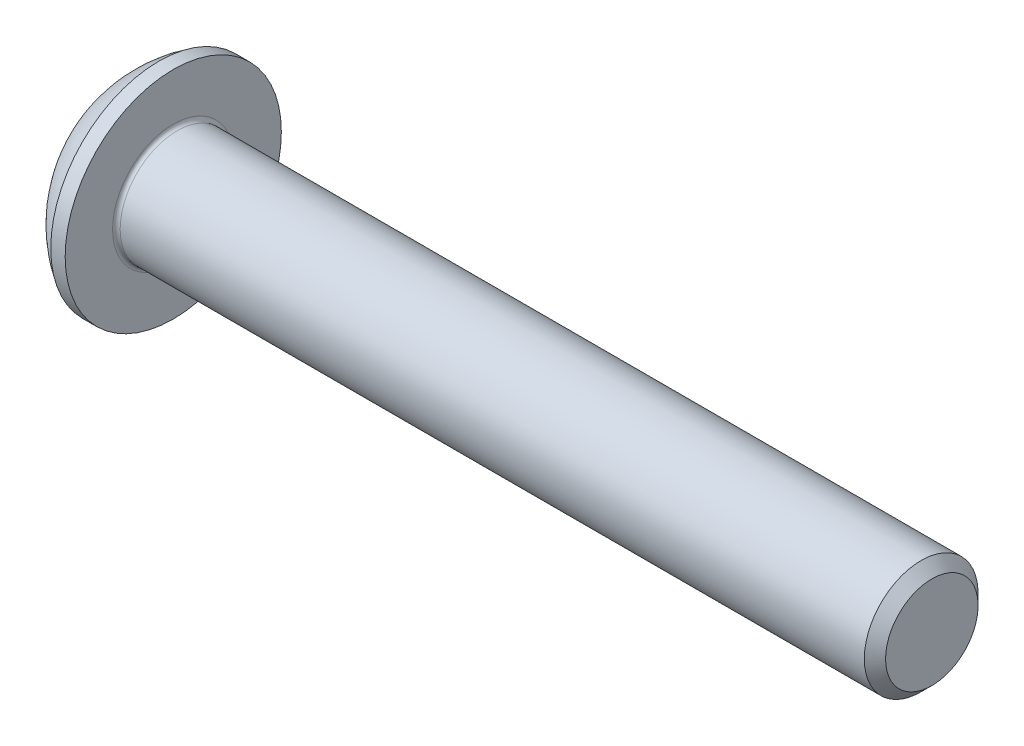
SolidWorks part; units mm, degrees
material "AISI 1035 鋼 (SS)"
ref_plane "Plane1" through (0, 0, 0) normal (0, 0, 1) x (1, 0, 0)
ref_plane "Plane2" through (0, 0, 0) normal (0, 1, 0) x (1, 0, 0)
ref_plane "Plane3" through (0, 0, 0) normal (1, 0, 0) x (0, 0, -1)
sketch "BodySke" plane through (0, 0, 0) normal (0, 0, 1) x (1, 0, 0)
  line L0 (21.65, 0) -> (21.65, 1.2195)
  line L1 (21.3695, 1.5) -> (1.65, 1.5)
  line L2 (1.65, 1.5) -> (1.65, 2.85)
  line L3 (1.65, 2.85) -> (1.27, 2.85)
  line L4 (0, 0) -> (101.6, 0) construction
  line L5 (1.65, -2.85) -> (1.27, -2.85) construction
  line L6 (55.6768, -1.5) -> (1.65, -1.5) construction
  line L7 (21.65, 0) -> (0, 0)
  line L8 (0, 1.425) -> (0, -1.425) construction
  line L9 (0, 0) -> (0, 1.425)
  line L10 (21.65, 1.2195) -> (21.3695, 1.5)
  line L11 (21.65, -1.2195) -> (21.3695, -1.5) construction
  line L12 (2.15, 9.525) -> (2.15, -1.5) construction
  line L13 (9.65, 9.525) -> (9.65, -1.5) construction
  arc A1 (0, 1.425) -> (1.27, 2.85) centre (3.0334, 0) cw
  dimension "Head_side_ht" = 0.38
  dimension "Body_ch_ang" = 45
revolve "BaseBody" add sketch "BodySke" angle 360 about L4
cosmetic thread "ThreadCosmetic" [suppressed] parameters "Thread_length"=12, "Thread_minor"=2.439
fillet "Fillet1" radius 0.1 1 edges at (1.65, 0, 1.5)
sketch "Sketch2" plane through (0, 0, 0) normal (0, 0, 1) x (1, 0, 0)
  line L0 (0, 1) -> (1.04, 1)
  line L1 (1.04, 1) -> (1.6174, 0)
  line L3 (1.6174, 0) -> (0, 0)
  line L4 (0, 0) -> (0, 1)
  line L5 (0, -1) -> (1.04, -1) construction
  line L6 (0, 0) -> (47.625, 0) construction
  dimension "D2" = 60
  dimension "PreBroach_depth" = 1.04
  dimension "PreBroach_dia" = 2
revolve "PreBroach" cut sketch "Sketch2" angle 360 about L6
sketch "Sketch3" plane through (0, 0, 0) normal (1, 0, 0) x (0, 0, -1)
  line L0 (-1, -0.5774) -> (-1, 0.5774)
  line L1 (-1, 0.5774) -> (0, 1.1547)
  line L2 (0, 1.1547) -> (1, 0.5774)
  line L3 (1, 0.5774) -> (1, -0.5774)
  line L4 (1, -0.5774) -> (0, -1.1547)
  line L5 (0, -1.1547) -> (-1, -0.5774)
extrude "Hex" cut sketch "Sketch3" along normal blind 1.04
sketch "ThdSchSke" plane through (0, 0, 0) normal (0, 0, 1) x (1, 0, 0)
  line L0 (9.65, -1.2195) -> (9.4536, -1.5)
  line L1 (9.65, -1.2195) -> (9.8464, -1.5)
  line L2 (9.8464, -1.5) -> (9.8464, -1.875)
  line L3 (-3.175, 0) -> (5.1513, 0) construction
  line L5 (9.8464, -1.875) -> (9.4536, -1.875)
  line L6 (9.4536, -1.875) -> (9.4536, -1.5)
  dimension "SideAngle" = 55
  dimension "VeeAngle" = 70
revolve "ThreadSchematic" [suppressed] cut sketch "ThdSchSke" angle 360 about L3
pattern_linear "ThdSchPat" [suppressed]
equation "\"D1@BodySke\" = \"Head_dia@BodySke\" * .5"
equation "\"Thread_minor@ThreadCosmetic\" = \"Minor_dia@BodySke\""
equation "\"D1@Sketch3\" = \"Hex_size@Sketch3\" / 2"
equation "\"D2@Sketch3\" = \"D1@Sketch3\""
equation "\"D3@Sketch3\" = \"Hex_size@Sketch3\""
equation "\"Thread_length@ThreadCosmetic\" = ((sgn( (\"Length@BodySke\" - \"Advance@BodySke\" * 2.0) - \"Thread_nom@BodySke\" )-1)*( (\"Length@BodySke\" - \"Advance@BodySke\" * 2.0) - \"Thread_nom@BodySke\" ))/-2+ \"Thread_nom@BodySke\""
equation "\"Thread_minor@ThdSchSke\" = \"Minor_dia@BodySke\""
equation "\"Diameter@ThdSchSke\" = \"Diameter@BodySke\""
equation "\"Overcut@ThdSchSke\" = \"Diameter@BodySke\" * 1.25"
equation "\"Start@ThdSchSke\" = \"Head_ht@BodySke\" + \"Length@BodySke\" - \"Thread_length@ThreadCosmetic\"  '---Non-countersunk---"
equation "\"Num_threads@ThdSchPat\" = int( \"Thread_length@ThreadCosmetic\" / \"Advance@BodySke\" + 0.999 )  + 1"
equation "\"Advance@ThdSchPat\" = \"Thread_length@ThreadCosmetic\" /  (\"Num_threads@ThdSchPat\" - 1) 'relax it"
equation "\"Num_threads@ThdSchPat\" = \"Num_threads@ThdSchPat\" - sgn( \"Num_threads@ThdSchPat\" - 1) '---chamfered tips only---"
